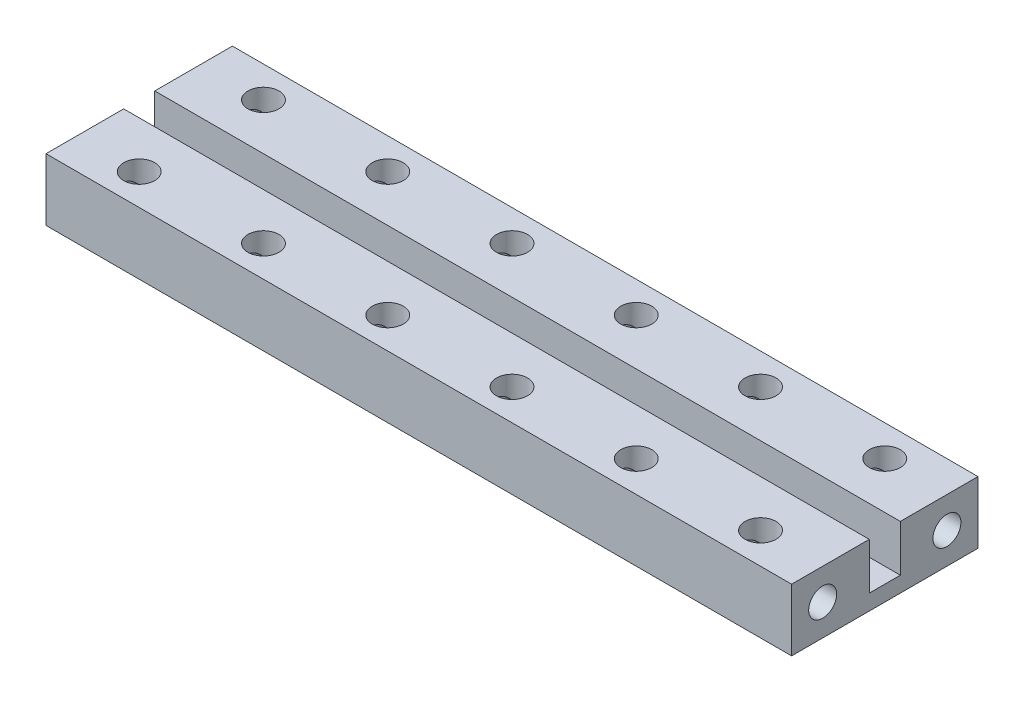
SolidWorks part; units mm, degrees
ref_plane "Front Plane" through (0, 0, 0) normal (0, 0, 1) x (1, 0, 0)
ref_plane "Top Plane" through (0, 0, 0) normal (0, 1, 0) x (1, 0, 0)
ref_plane "Right Plane" through (0, 0, 0) normal (1, 0, 0) x (0, 0, -1)
sketch "스케치1" plane through (0, 0, 0) normal (0, 1, 0) x (1, 0, 0)
  line L1 (-48, 12) -> (48, 12)
  line L2 (-48, 12) -> (-48, -12)
  line L3 (-48, -12) -> (48, -12)
  line L4 (48, 12) -> (48, -12)
  dimension "D1" = 48
  dimension "D2" = 96
  dimension "D3" = 12
  dimension "D4" = 24
extrude "보스-돌출1" add sketch "스케치1" along normal blind 8
sketch "스케치2" plane through (0, 8, 0) normal (0, 1, 0) x (1, 0, 0)
  line L0 (0, 0) -> (50000, 0) construction
  line L1 (-26.8589, 2) -> (49973.1411, 2) construction
  line L2 (-23.8852, -2) -> (49976.1148, -2) construction
  line L3 (-48, 12) -> (-48, -12) construction
  line L4 (-48, 2) -> (48, 2)
  line L5 (-48, 2) -> (-48, -2)
  line L6 (-48, -2) -> (48, -2)
  line L7 (48, 2) -> (48, -2)
  line L8 (48, -12) -> (48, 12) construction
  dimension "D1" = 2
  dimension "D2" = 2
extrude "컷-돌출1" cut sketch "스케치2" against normal blind 6
sketch "스케치3" plane through (-48, 0, 0) normal (-1, 0, 0) x (0, 0, 1)
  line L0 (-9.3766, 4) -> (49990.6234, 4) construction
  line L1 (-8, 5.7626) -> (-8, -49994.2374) construction
  line L2 (8, 6.1463) -> (8, -49993.8537) construction
  line L3 (-12, 0) -> (12, 0) construction
  circle A0 centre (-8, 4) radius 1.8
  circle A1 centre (8, 4) radius 1.8
  dimension "D1" = 4
  dimension "D2" = 8
  dimension "D3" = 8
extrude "컷-돌출2" cut sketch "스케치3" against normal through all
sketch "스케치4" plane through (0, 8, 0) normal (0, 1, 0) x (1, 0, 0)
  line L0 (-40, 18.8492) -> (-40, -49981.1508) construction
  line L1 (-24, 14.5326) -> (-24, -49985.4674) construction
  line L2 (-8, 25.6598) -> (-8, -49974.3402) construction
  line L3 (8, 26.9068) -> (8, -49973.0932) construction
  line L5 (-57.0751, 8) -> (49942.9249, 8) construction
  line L6 (24, 30.8398) -> (24, -49969.1602) construction
  line L7 (40, 34.6767) -> (40, -49965.3233) construction
  line L8 (-48, 12) -> (-48, 2) construction
  line L9 (-58.2262, -8) -> (49941.7738, -8) construction
  circle A0 centre (-40, 8) radius 2
  circle A1 centre (-24, 8) radius 2
  circle A2 centre (-40, -8) radius 2
  circle A3 centre (-24, -8) radius 2
  circle A4 centre (-8, 8) radius 2
  circle A5 centre (-8, -8) radius 2
  circle A6 centre (8, 8) radius 2
  circle A7 centre (8, -8) radius 2
  circle A8 centre (24, 8) radius 2
  circle A9 centre (24, -8) radius 2
  circle A10 centre (40, -8) radius 2
  circle A11 centre (40, 8) radius 2
  dimension "D1" = 8
  dimension "D2" = 16
  dimension "D3" = 16
  dimension "D4" = 16
  dimension "D5" = 16
  dimension "D6" = 16
  dimension "D7" = 8
  dimension "D8" = 8
extrude "컷-돌출3" cut sketch "스케치4" against normal through all
